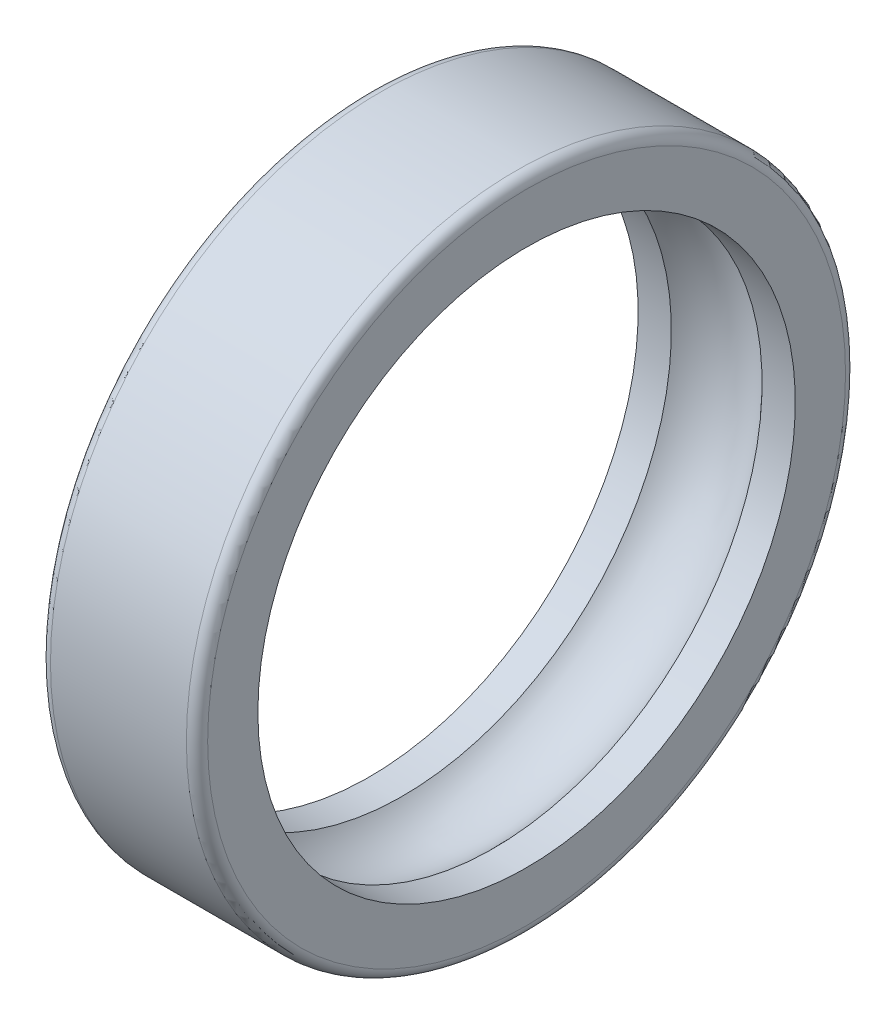
SolidWorks part; units mm, degrees
ref_plane "Front Plane" through (0, 0, 0) normal (0, 0, 1) x (1, 0, 0)
ref_plane "Top Plane" through (0, 0, 0) normal (0, 1, 0) x (1, 0, 0)
ref_plane "Right Plane" through (0, 0, 0) normal (1, 0, 0) x (0, 0, -1)
sketch "Sketch1" plane through (0, 0, 0) normal (0, 0, 1) x (1, 0, 0)
  line L0 (-12.8091, 0) -> (14.6901, 0) construction
  line L1 (0, 0) -> (0, 53) construction
  line L2 (-15.5, 65) -> (15.5, 65)
  line L3 (-15.5, 65) -> (-15.5, 53)
  line L4 (-15.5, 53) -> (-8.9443, 53)
  line L5 (15.5, 65) -> (15.5, 53)
  line L6 (-15.5, 65) -> (15.5, 53) construction
  line L7 (-15.5, 53) -> (15.5, 65) construction
  line L8 (8.9443, 53) -> (15.5, 53)
  arc A0 (-8.9443, 53) -> (8.9443, 53) centre (0, 45) cw
  point P3 (0, 59)
  dimension "D5" = 12
  dimension "D1" = 31
  dimension "D2" = 53
  dimension "D3" = 65
  dimension "D4" = 8
revolve "Revolve1" add sketch "Sketch1" angle 360 about L0
fillet "Fillet1" radius 2.1 2 edges at (15.5, 0, 65) (-15.5, 0, 65)
scale "Scale1" scale about centroid uniform scaling yes scale factor 1.2
scale "Scale2" scale about centroid uniform scaling yes scale factor 0.1
